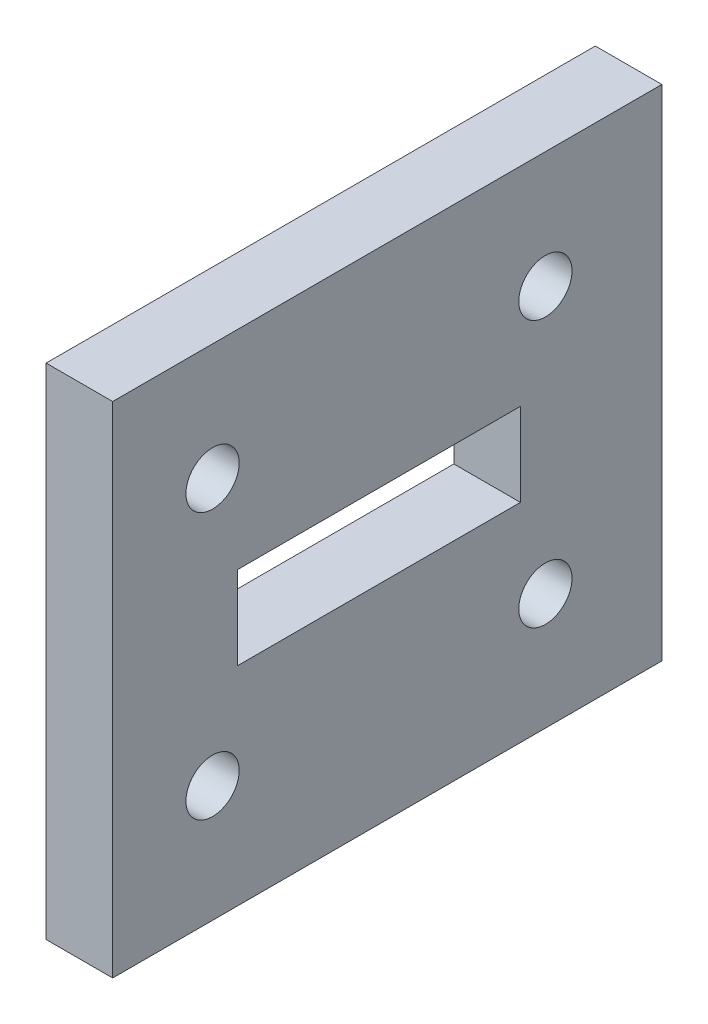
SolidWorks part; units mm, degrees
ref_plane "Спереди" through (0, 0, 0) normal (0, 0, 1) x (1, 0, 0)
ref_plane "Сверху" through (0, 0, 0) normal (0, 1, 0) x (1, 0, 0)
ref_plane "Справа" through (0, 0, 0) normal (1, 0, 0) x (0, 0, -1)
ref_plane "Плоскость4" through (15.4739, 0, 0) normal (1, 0, 0) x (0, 0, -1)
sketch "Эскиз1" plane through (15.4739, 0, 0) normal (1, 0, 0) x (0, 0, -1)
  line L4 (-13.2363, 38.4936) -> (-13.2363, 8.4936)
  line L5 (-13.2363, 38.4936) -> (-13.2363, 8.4936)
  line L6 (-13.2363, 8.4936) -> (19.7637, 8.4936)
  line L7 (-13.2363, 8.4936) -> (19.7637, 8.4936)
  line L8 (19.7637, 8.4936) -> (19.7637, 38.4936)
  line L9 (19.7637, 8.4936) -> (19.7637, 38.4936)
  line L10 (19.7637, 38.4936) -> (-13.2363, 38.4936)
  line L11 (19.7637, 38.4936) -> (-13.2363, 38.4936)
  circle A0 centre (-7.2363, 31.4936) radius 1.6 construction
  circle A1 centre (12.7637, 31.4936) radius 1.6 construction
  circle A2 centre (-7.2363, 15.4936) radius 1.6 construction
  circle A3 centre (12.7637, 15.4936) radius 1.6 construction
  circle A4 centre (-7.2363, 31.4936) radius 1.6
  circle A5 centre (12.7637, 31.4936) radius 1.6
  circle A6 centre (-7.2363, 15.4936) radius 1.6
  circle A7 centre (12.7637, 15.4936) radius 1.6
  dimension "D1" = 0
extrude "Бобышка-Вытянуть1" add sketch "Эскиз1" along normal blind 4
sketch "Sketch2" plane through (15.4739, 0, 0) normal (-1, 0, 0) x (0, 0, 1)
  line L0 (-11.2637, 25.9936) -> (-11.2637, 20.9936)
  line L1 (-11.2637, 25.9936) -> (5.7363, 25.9936)
  line L2 (-11.2637, 20.9936) -> (5.7363, 20.9936)
  line L3 (5.7363, 25.9936) -> (5.7363, 20.9936)
  line L4 (-12.7637, 31.4936) -> (7.2363, 31.4936) construction
  line L5 (-12.7637, 31.4936) -> (-12.7637, 15.4936) construction
  line L6 (7.2363, 31.4936) -> (7.2363, 15.4936) construction
  line L7 (-12.7637, 15.4936) -> (7.2363, 15.4936) construction
  line L8 (-2.7637, 31.4936) -> (-2.7637, 15.4936) construction
  line L9 (-2.7637, 25.9936) -> (-2.7637, 20.9936) construction
  line L10 (7.2363, 23.4936) -> (-12.7637, 23.4936) construction
  line L11 (5.7363, 23.4936) -> (-11.2637, 23.4936) construction
  circle A0 centre (-12.7637, 15.4936) radius 1.6 construction
  circle A1 centre (-12.7637, 15.4936) radius 1.6 construction
  dimension "D1" = 17
  dimension "D2" = 5
extrude "Cut-Extrude2" cut sketch "Sketch2" against normal through all
